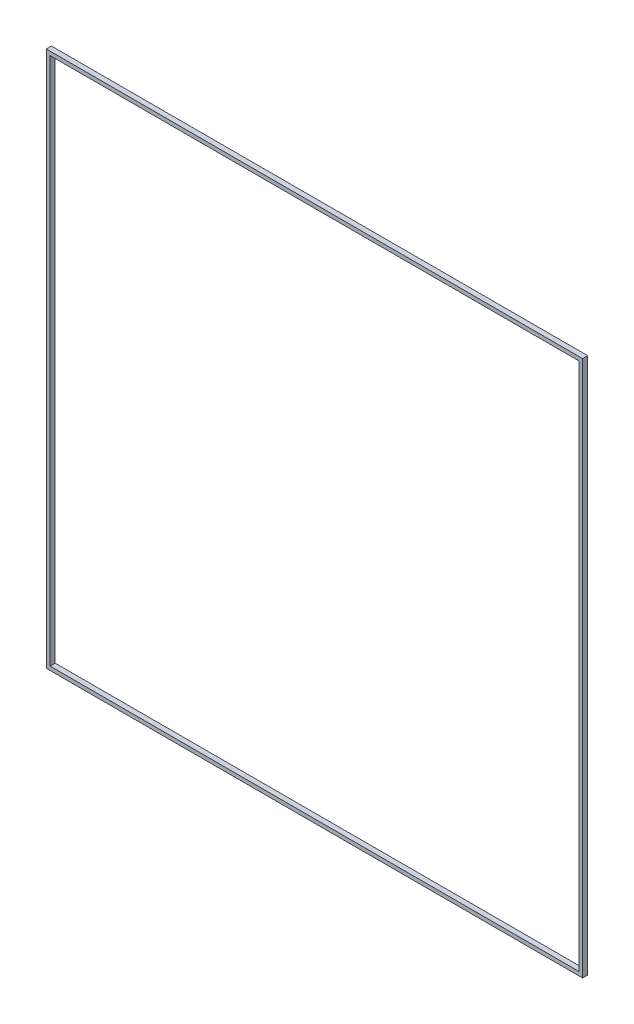
SolidWorks part; units mm, degrees
ref_plane "Front Plane" through (0, 0, 0) normal (0, 0, 1) x (1, 0, 0)
ref_plane "Top Plane" through (0, 0, 0) normal (0, 1, 0) x (1, 0, 0)
ref_plane "Right Plane" through (0, 0, 0) normal (1, 0, 0) x (0, 0, -1)
sketch "Sketch1" plane through (0, 0, 0) normal (0, 0, 1) x (1, 0, 0)
  line L5 (-100, -100) -> (100, 100) construction
  line L6 (-100, 100) -> (100, -100) construction
  line L7 (-105, -105) -> (105, -105)
  line L8 (-105, -105) -> (-105, 105)
  line L9 (-105, 105) -> (105, 105)
  line L10 (105, -105) -> (105, 105)
  line L11 (-105, -105) -> (105, 105) construction
  line L12 (-105, 105) -> (105, -105) construction
  point P0 (0, 0)
  point P6 (0, 0)
  dimension "D3" = 210
  dimension "D4" = 210
extrude "Boss-Extrude1" add sketch "Sketch1" along normal blind 2
sketch "Sketch2" plane through (0, 0, 2) normal (0, 0, 1) x (1, 0, 0)
  line L1 (-103.5, -103.5) -> (103.5, -103.5)
  line L2 (-103.5, -103.5) -> (-103.5, 103.5)
  line L3 (-103.5, 103.5) -> (103.5, 103.5)
  line L4 (103.5, -103.5) -> (103.5, 103.5)
  line L5 (-103.5, -103.5) -> (103.5, 103.5) construction
  line L6 (-103.5, 103.5) -> (103.5, -103.5) construction
  point P0 (0, 0)
  dimension "D1" = 207
  dimension "D2" = 207
extrude "Cut-Extrude2" cut sketch "Sketch2" against normal through all contours L2 L1 L4 L3
